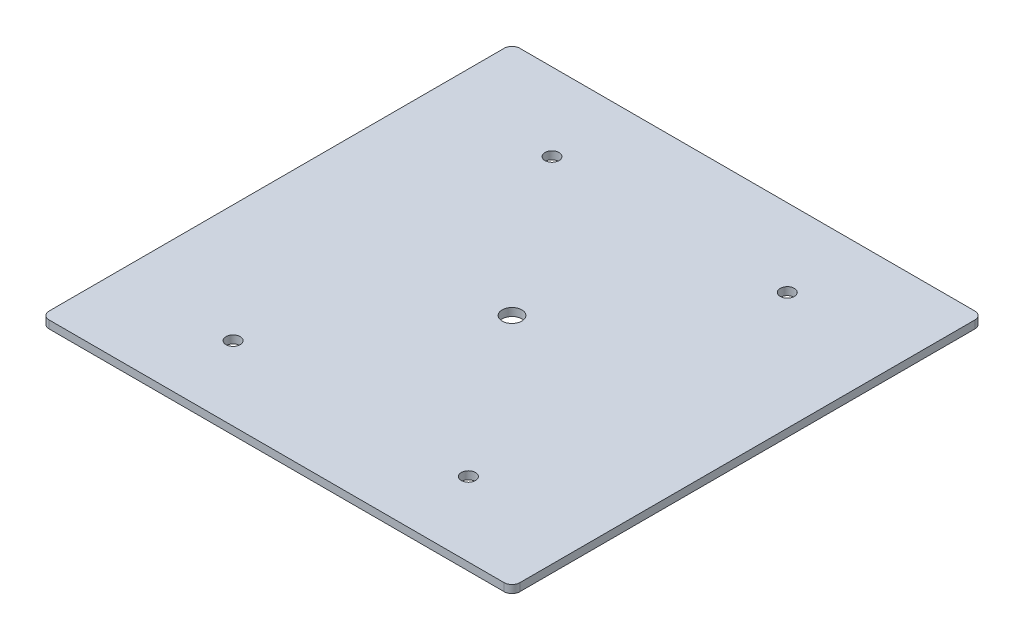
SolidWorks part; units mm, degrees
material "ASTM A36 Steel"
ref_plane "Front Plane" through (0, 0, 0) normal (0, 0, 1) x (1, 0, 0)
ref_plane "Top Plane" through (0, 0, 0) normal (0, 1, 0) x (1, 0, 0)
ref_plane "Right Plane" through (0, 0, 0) normal (1, 0, 0) x (0, 0, -1)
sketch "Sketch1" plane through (0, 0, 0) normal (0, 1, 0) x (1, 0, 0)
  line L1 (-73.66, 76.2) -> (73.66, 76.2)
  line L2 (-76.2, 73.66) -> (-76.2, -73.66)
  line L3 (-73.66, -76.2) -> (73.66, -76.2)
  line L4 (76.2, 73.66) -> (76.2, -73.66)
  line L5 (-76.2, 76.2) -> (76.2, -76.2) construction
  line L6 (-76.2, -76.2) -> (76.2, 76.2) construction
  arc A0 (-76.2, 73.66) -> (-73.66, 76.2) centre (-73.66, 73.66) cw
  arc A1 (76.2, 73.66) -> (73.66, 76.2) centre (73.66, 73.66) ccw
  arc A2 (-73.66, -76.2) -> (-76.2, -73.66) centre (-73.66, -73.66) cw
  arc A3 (76.2, -73.66) -> (73.66, -76.2) centre (73.66, -73.66) cw
  circle A4 centre (0, 0) radius 1.4224
  point P0 (0, 0)
  dimension "D3" = 2.54
  dimension "D4" = 2.54
  dimension "D5" = 2.54
  dimension "D6" = 2.54
  dimension "D1" = 152.4
  dimension "D2" = 152.4
extrude "Boss-Extrude1" add sketch "Sketch1" along normal blind 2.54
sketch "Sketch2" plane through (0, 2.54, 0) normal (0, 1, 0) x (1, 0, 0)
  circle A0 centre (-38.1, 51.0515) radius 2.286
  circle A1 centre (38.1, 51.0515) radius 2.286
  circle A2 centre (38.1, -52.2217) radius 2.286
  circle A3 centre (-38.1, -52.2217) radius 2.286
  circle A4 centre (0, 0) radius 3.175
  dimension "D3" = 6.35
  dimension "D4" = 4.572
  dimension "D5" = 4.572
  dimension "D6" = 4.572
  dimension "D7" = 4.572
  dimension "D1" = 76.2
  dimension "D2" = 38.1
extrude "Cut-Extrude1" cut sketch "Sketch2" against normal through all
